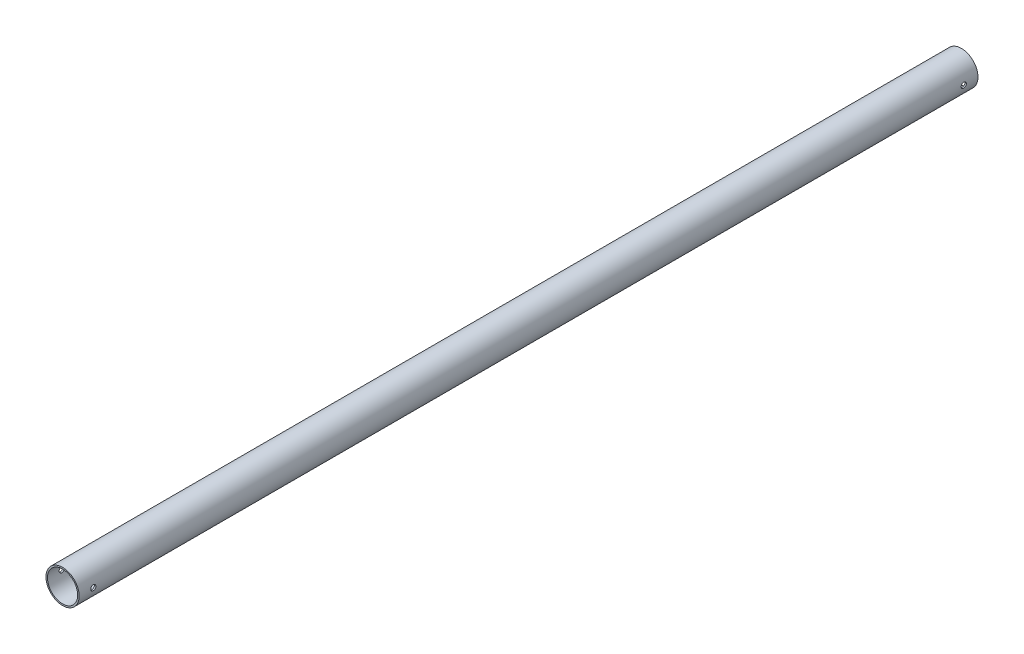
SolidWorks part; units mm, degrees
material "1060 Alloy"
ref_plane "Front Plane" through (0, 0, 0) normal (0, 0, 1) x (1, 0, 0)
ref_plane "Top Plane" through (0, 0, 0) normal (0, 1, 0) x (1, 0, 0)
ref_plane "Right Plane" through (0, 0, 0) normal (1, 0, 0) x (0, 0, -1)
sketch "Sketch2" plane through (0, 0, 0) normal (0, 0, 1) x (1, 0, 0)
  circle A0 centre (0, 0) radius 17.5
  circle A1 centre (0, 0) radius 15.9125
  dimension "D1" = 35
  dimension "D2" = 31.825
extrude "Boss-Extrude1" add sketch "Sketch2" along normal mid plane 948
sketch "Sketch3" plane through (0, 0, 0) normal (1, 0, 0) x (0, 0, -1)
  line L2 (474, 0) -> (459, 0) construction
  line L3 (474, -17.5) -> (474, 17.5) construction
  dimension "D1" = 15
hole_wizard "M5 Clearance Hole1" positions "Sketch4" profile "Sketch5" hole size "M5" standard "AS"
sketch "Sketch4" plane through (0, 0, 0) normal (1, 0, 0) x (0, 0, -1)
  point P0 (459, 0)
sketch "Sketch5" plane through (0, 0, -459) normal (0, 1, 0) x (0, 0, 1)
  line L0 (0, 0) -> (0, 17.5)
  line L1 (0, 17.5) -> (2.75, 17.5)
  line L2 (2.75, 17.5) -> (2.75, 0)
  line L5 (2.75, 0) -> (0, 0)
  line L11 (0, -6.35) -> (0, 107.95) construction
  dimension "Thru Hole Dia." = 5.5
  dimension "Thru Hole Depth" = 17.5
mirror "Mirror1" about plane through (0, 0, 0) normal (0, 0, 1) of "M5 Clearance Hole1" second plane through (0, 0, 0) second plane normal (1, 0, 0)
equation "\"frontTubeLength\"= 1200mm"
equation "\"outDiameter\"= 35mm"
equation "\"keelOutDiameter\"= 1in"
equation "\"bottomTubeLength\"= \"frontTubeLength\"*0.9"
equation "\"D1@Sketch2\"=\"outDiameter\""
equation "\"D2@Sketch2\"=\"outDiameter\"-0.125in"
equation "\"D1@Boss-Extrude1\"=\"frontTubeLength\"*0.79"
